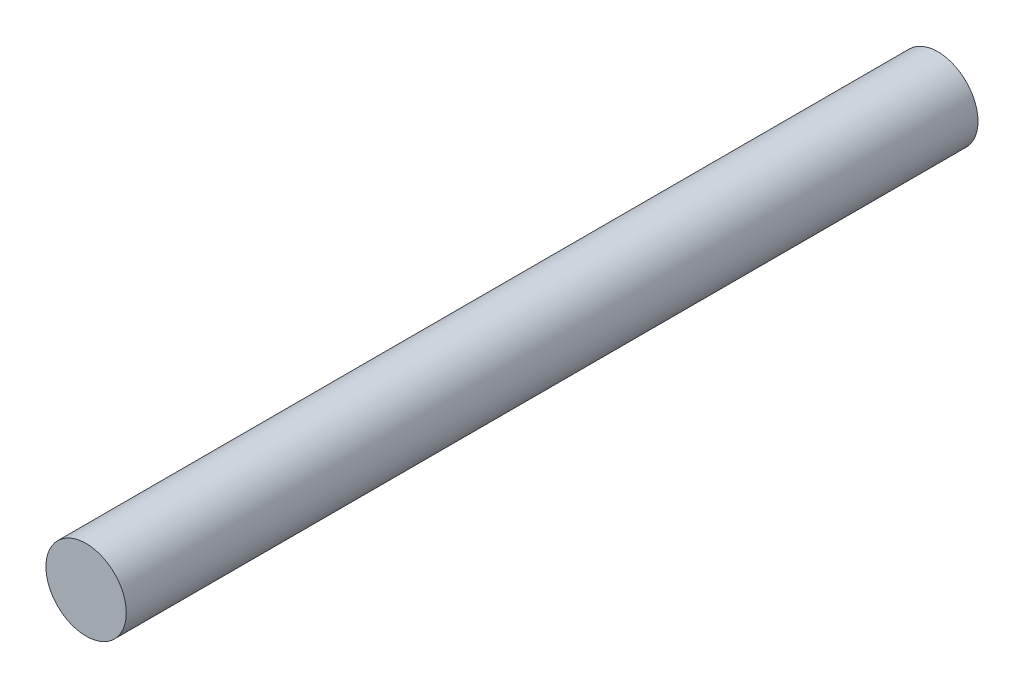
SolidWorks part; units mm, degrees
material "PLA"
ref_plane "Front Plane" through (0, 0, 0) normal (0, 0, 1) x (1, 0, 0)
ref_plane "Top Plane" through (0, 0, 0) normal (0, 1, 0) x (1, 0, 0)
ref_plane "Right Plane" through (0, 0, 0) normal (1, 0, 0) x (0, 0, -1)
sketch "Sketch1" plane through (0, 0, 0) normal (0, 0, 1) x (1, 0, 0)
  circle A0 centre (0, 0) radius 2.5
extrude "Boss-Extrude1" add sketch "Sketch1" along normal mid plane 53
